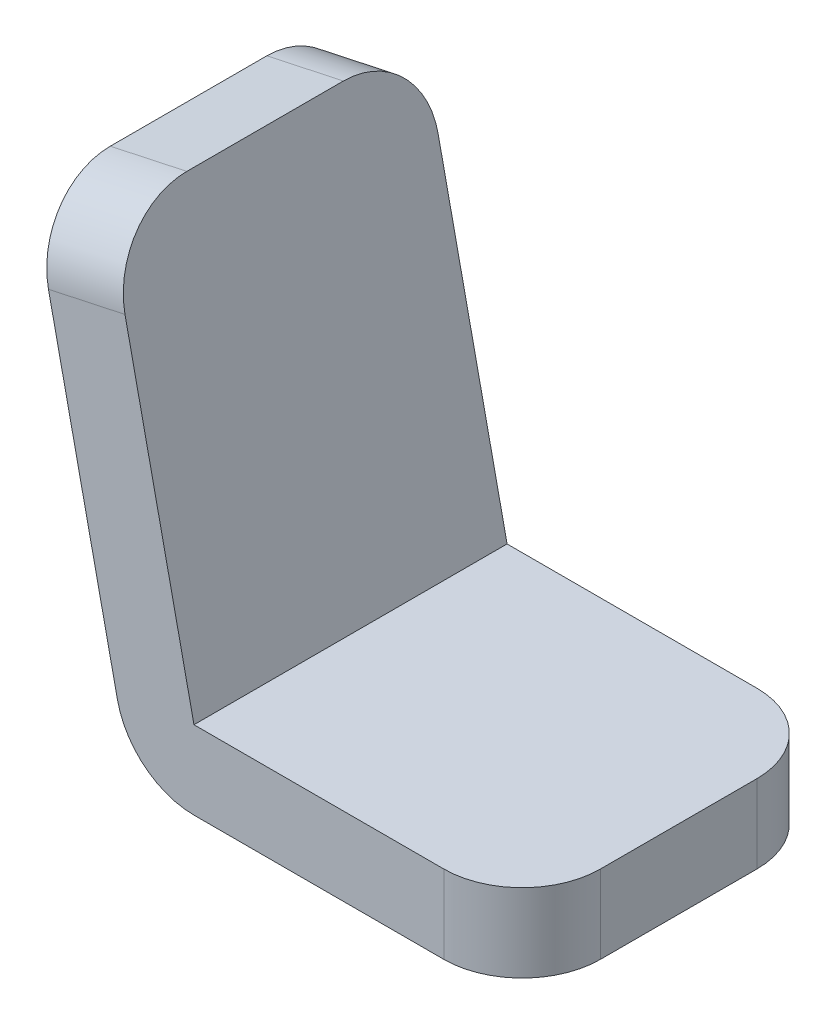
SolidWorks part; units mm, degrees
ref_plane "Front Plane" through (0, 0, 0) normal (0, 0, 1) x (1, 0, 0)
ref_plane "Top Plane" through (0, 0, 0) normal (0, 1, 0) x (1, 0, 0)
ref_plane "Right Plane" through (0, 0, 0) normal (1, 0, 0) x (0, 0, -1)
sketch "Sketch1" plane through (0, 0, 0) normal (0, 0, 1) x (1, 0, 0)
  line L0 (50, 0) -> (8.0788, 0)
  line L1 (-1.6979, 7.8984) -> (-12.6098, 58.66)
  arc A0 (8.0788, 0) -> (-1.6979, 7.8984) centre (8.0788, 10) cw
  point P6 (0, 0)
  dimension "D3" = 10
  dimension "D1" = 50
  dimension "D2" = 60
extrude "Extrude-Thin1" add sketch "Sketch1" along normal blind 40 thin
fillet "Fillet1" radius 10 1 edges at (-7.7214, 59.7108, 40)
fillet "Fillet2" radius 10 1 edges at (50, 5, 40)
fillet "Fillet3" radius 10 1 edges at (50, 5, 0)
fillet "Fillet4" radius 10 1 edges at (-7.7214, 59.7108, 0)
